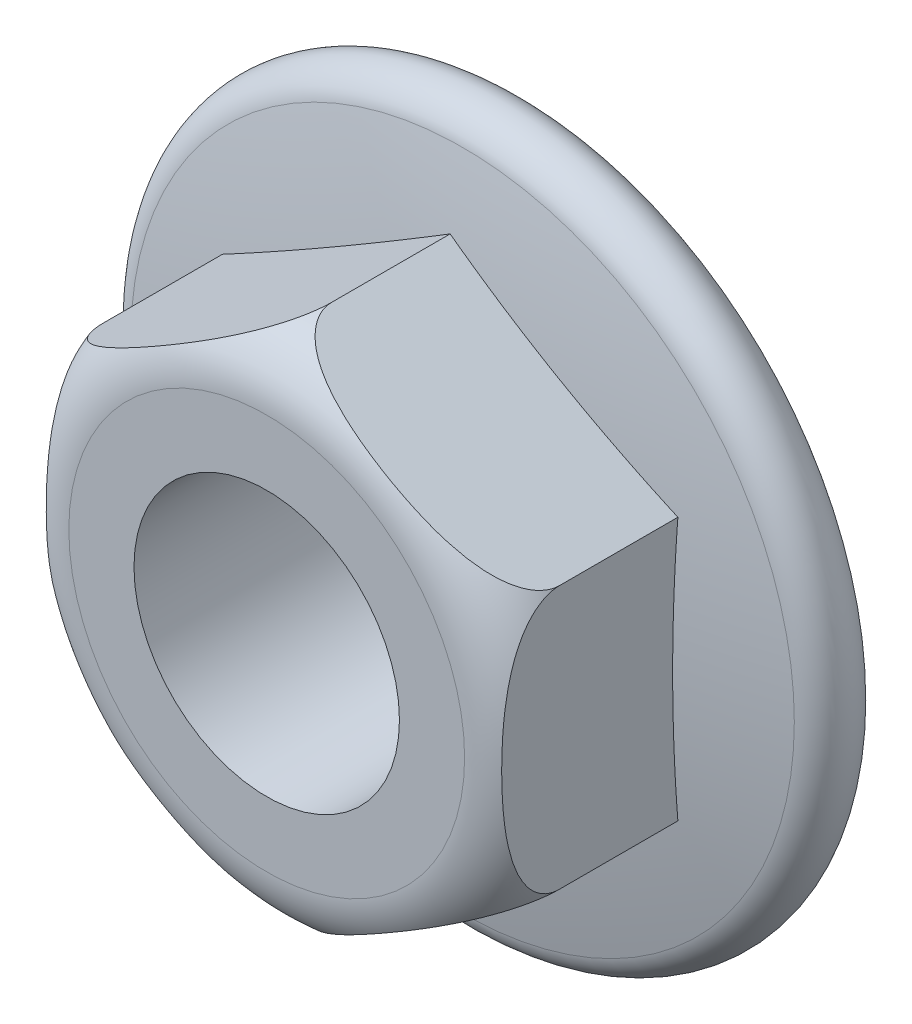
SolidWorks part; units mm, degrees
ref_plane "Plane1" through (0, 0, 0) normal (0, 0, 1) x (1, 0, 0)
ref_plane "Plane2" through (0, 0, 0) normal (0, 1, 0) x (-1, 0, 0)
ref_plane "Plane3" through (0, 0, 0) normal (1, 0, 0) x (0, 0, -1)
other "Configuration Table"
sketch "Head Sketch" plane through (0, 0, 0) normal (0, 0, 1) x (1, 0, 0)
  line L0 (0, 4.0415) -> (3.5, 2.0207)
  line L1 (3.5, 2.0207) -> (3.5, -2.0207)
  line L2 (3.5, -2.0207) -> (0, -4.0415)
  line L3 (0, -4.0415) -> (-3.5, -2.0207)
  line L4 (-3.5, -2.0207) -> (-3.5, 2.0207)
  line L5 (-3.5, 2.0207) -> (0, 4.0415)
  line L6 (3.5, 2.0207) -> (-3.5, -2.0207) construction
  line L7 (0, 4.0415) -> (0, -4.0415) construction
  line L8 (-3.5, 2.0207) -> (3.5, -2.0207) construction
  point P0 (0, 0)
  dimension "D1" = 60
  dimension "D2" = 60
  dimension "Flats" = 7
extrude "Head" add sketch "Head Sketch" along normal blind 4
sketch "Flange Sketch" plane through (0, 0, 0) normal (0, 1, 0) x (-1, 0, 0)
  line L0 (0, 1.8434) -> (0, 1.5) construction
  line L1 (-5, 0) -> (0, 0)
  line L2 (0, 50) -> (0, -50) construction
  line L4 (0, 0) -> (0, 1.5)
  line L5 (0, 0) -> (-3.5, 0) construction
  arc A0 (0, 1.5) -> (-5.099, 0.9901) centre (0, -24.25) ccw
  arc A1 (-5, 0) -> (-5.099, 0.9901) centre (-5, 0.5) cw
  dimension "D1" = 0.5
  dimension "D3" = 10
  dimension "Flange Height" = 1.5
revolve "Flange" add sketch "Flange Sketch" angle 360 about L0
sketch "Sketch5" plane through (0, 0, 0) normal (1, 0, 0) x (0, 0, -1)
  line L0 (-4, -3.0415) -> (-4, -4.0415)
  line L1 (-4, -4.0415) -> (-3, -4.0415)
  line L2 (-4, -4.0415) -> (-1.1809, -4.0415) construction
  line L3 (-4, -4.0415) -> (-4, -2.0207) construction
  line L5 (-15.0856, 0) -> (-8.1394, 0) construction
  line L6 (50, 0) -> (-50, 0) construction
  arc A0 (-4, -3.0415) -> (-3, -4.0415) centre (-3, -3.0415) ccw
  dimension "D1" = 1
revolve "Head Trim" cut sketch "Sketch5" angle 360 about L5
sketch "Hole Sketch" plane through (0, 0, 4) normal (0, 0, 1) x (1, 0, 0)
  line L0 (50, 0) -> (-50, 0) construction
  line L1 (0, -50) -> (0, 50) construction
  circle A0 centre (0, 0) radius 2.04
  dimension "Hole Dia" = 4.08
extrude "Through Hole" cut sketch "Hole Sketch" against normal through all
